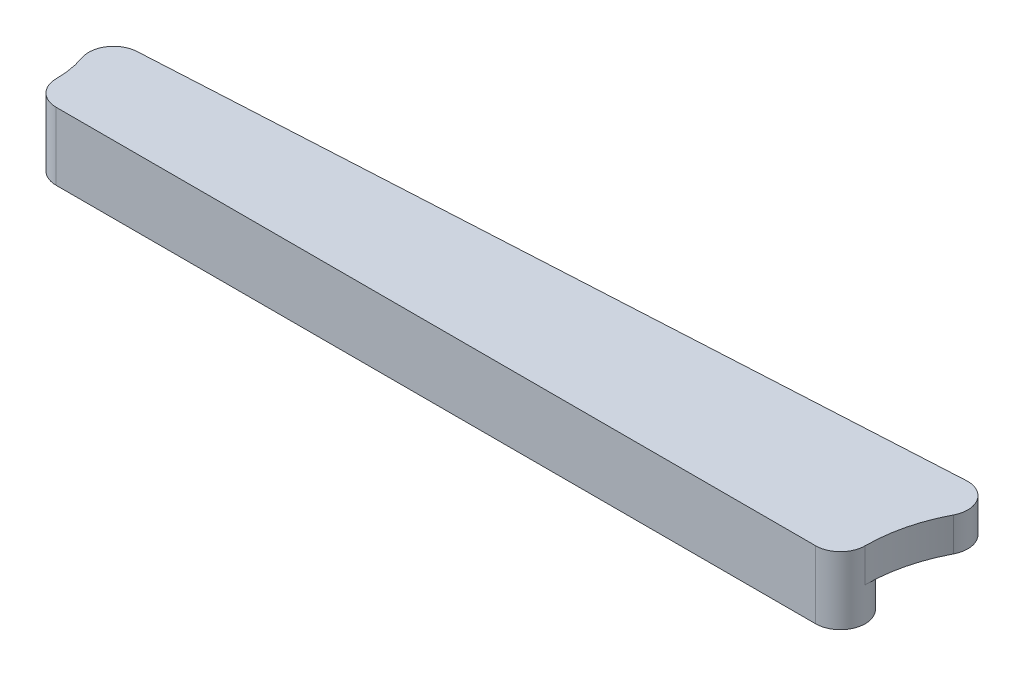
SolidWorks part; units mm, degrees
material "ABS"
ref_plane "Front Plane" through (0, 0, 0) normal (0, 0, 1) x (1, 0, 0)
ref_plane "Top Plane" through (0, 0, 0) normal (0, 1, 0) x (1, 0, 0)
ref_plane "Right Plane" through (0, 0, 0) normal (1, 0, 0) x (0, 0, -1)
sketch "Sketch1" plane through (0, 0, 0) normal (0, 1, 0) x (1, 0, 0)
  line L0 (-73.025, 0) -> (73.025, 0) construction
  line L1 (-73.025, 4.7625) -> (73.025, 4.7625)
  line L2 (-73.025, -4.7625) -> (73.025, -4.7625)
  arc A0 (-73.025, 4.7625) -> (-73.025, -4.7625) centre (-73.025, 0) ccw
  arc A1 (73.025, -4.7625) -> (73.025, 4.7625) centre (73.025, 0) ccw
  point P2 (0, 0)
  dimension "D3" = 9.525
  dimension "D1" = 146.05
extrude "Boss-Extrude1" add sketch "Sketch1" along normal mid plane 13
sketch "Sketch3" plane through (0, 0, 0) normal (0, 1, 0) x (1, 0, 0)
  line L0 (-96.6515, 11.0959) -> (105.9408, 22.1917) construction
  line L1 (76.6589, 20.588) -> (-74.559, 12.3059)
  line L2 (73.025, 4.7625) -> (-73.025, 4.7625)
  line L3 (73.025, 4.7625) -> (-73.025, 4.7625) construction
  arc A0 (77.7875, 0) -> (81.1384, 13.6234) centre (107.1562, 0) cw
  arc A1 (73.025, -4.7625) -> (73.025, 4.7625) centre (73.025, 0) ccw construction
  arc A2 (81.1384, 13.6234) -> (76.6589, 20.588) centre (76.9193, 15.8326) ccw
  arc A3 (-77.7875, 0) -> (-78.7976, 5.9883) centre (-96.0438, 0) ccw
  arc A4 (-73.025, 4.7625) -> (-73.025, -4.7625) centre (-73.025, 0) ccw construction
  arc A5 (-78.7976, 5.9883) -> (-74.559, 12.3059) centre (-74.2986, 7.5505) cw
  arc A6 (77.7875, 0) -> (73.025, 4.7625) centre (73.025, 0) ccw
  arc A7 (-77.7875, 0) -> (-73.025, 4.7625) centre (-73.025, 0) cw
  point P23 (71.9014, 2.7287)
  point P26 (0, 0)
  dimension "D1" = 4.7625
extrude "Boss-Extrude2" add sketch "Sketch3" along normal up to surface (6.5 mm away) up to face at (0, 6.5, 0)
equation "\"Num_Holes\"=10"
equation "\"D1@LPattern1\"=\"Num_Holes\""
equation "\"thicknes\"= 13mm"
equation "\"D1@Boss-Extrude1\"=\"thicknes\""
